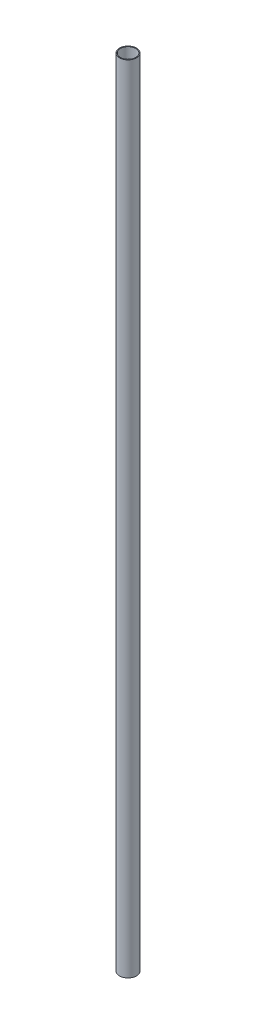
SolidWorks part; units mm, degrees
ref_plane "Front Plane" through (0, 0, 0) normal (0, 0, 1) x (1, 0, 0)
ref_plane "Top Plane" through (0, 0, 0) normal (0, 1, 0) x (1, 0, 0)
ref_plane "Right Plane" through (0, 0, 0) normal (1, 0, 0) x (0, 0, -1)
sketch "Sketch1" plane through (0, 0, 0) normal (0, 1, 0) x (1, 0, 0)
  circle A0 centre (0, 0) radius 9.525
  circle A1 centre (0, 0) radius 8.636
  dimension "D1" = 19.05
  dimension "D2" = 0.889
extrude "Boss-Extrude1" add sketch "Sketch1" along normal blind 889
